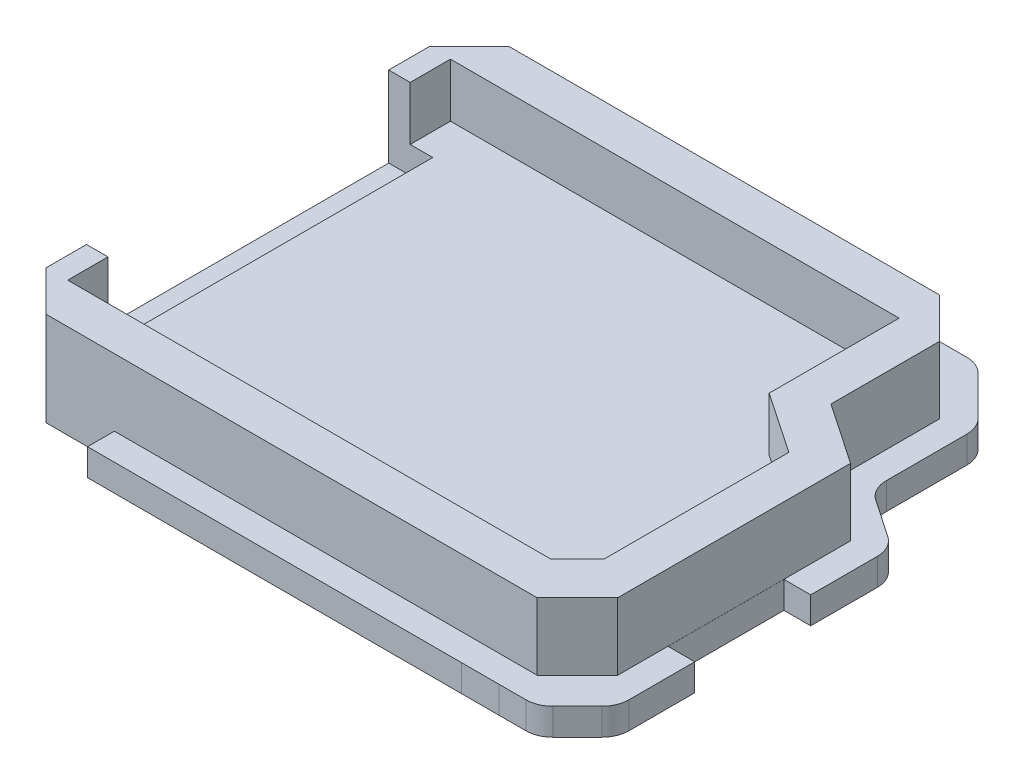
SolidWorks part; units mm, degrees
ref_plane "Front Plane" through (0, 0, 0) normal (0, 0, 1) x (1, 0, 0)
ref_plane "Top Plane" through (0, 0, 0) normal (0, 1, 0) x (1, 0, 0)
ref_plane "Right Plane" through (0, 0, 0) normal (1, 0, 0) x (0, 0, -1)
sketch "Sketch1" plane through (0, 0, 0) normal (0, 1, 0) x (1, 0, 0)
  line L0 (-34.6415, 17.5848) -> (-34.6415, -16.9152)
  line L1 (-31.6415, 14.5848) -> (3.3585, 14.5848)
  line L2 (-31.6415, 14.5848) -> (-31.6415, -13.9152)
  line L3 (-31.6415, -13.9152) -> (3.3585, -13.9152)
  line L4 (3.3585, 14.5848) -> (3.3585, -13.9152)
  line L5 (-34.6415, -16.9152) -> (6.3585, -16.9152)
  line L6 (6.3585, 17.5848) -> (6.3585, -16.9152)
  line L7 (-34.6415, 17.5848) -> (6.3585, 17.5848)
  dimension "D1" = 3
extrude "Boss-Extrude1" add sketch "Sketch1" along normal blind 5
sketch "Sketch2" plane through (0, 0, 0) normal (0, 1, 0) x (1, 0, 0)
  line L1 (-31.6415, 14.5848) -> (3.3585, 14.5848)
  line L2 (-31.6415, 14.5848) -> (-31.6415, -13.9152)
  line L3 (-31.6415, -13.9152) -> (3.3585, -13.9152)
  line L4 (3.3585, 14.5848) -> (3.3585, -13.9152)
extrude "Boss-Extrude2" add sketch "Sketch2" along normal blind 1
sketch "Sketch6" plane through (-34.6415, 0, 0) normal (-1, 0, 0) x (0, 0, 1)
  line L1 (-17.5848, 5) -> (16.9152, 5)
  line L2 (-17.5848, 5) -> (-17.5848, 0)
  line L3 (-17.5848, 0) -> (16.9152, 0)
  line L4 (16.9152, 5) -> (16.9152, 0)
extrude "Cut-Extrude2" cut sketch "Sketch6" against normal blind 3
sketch "Sketch7" plane through (0, 1, 0) normal (0, 1, 0) x (1, 0, 0)
  line L1 (-31.6415, 14.5848) -> (-30.0415, 14.5848)
  line L2 (-31.6415, 14.5848) -> (-31.6415, 11.5848)
  line L3 (-31.6415, 11.5848) -> (-30.0415, 11.5848)
  line L4 (-30.0415, 14.5848) -> (-30.0415, 11.5848)
  line L5 (-31.6415, -13.9152) -> (-30.0415, -13.9152)
  line L6 (-31.6415, -13.9152) -> (-31.6415, -10.9152)
  line L7 (-31.6415, -10.9152) -> (-30.0415, -10.9152)
  line L8 (-30.0415, -13.9152) -> (-30.0415, -10.9152)
extrude "Boss-Extrude3" add sketch "Sketch7" along normal blind 4
chamfer "Chamfer1" distance 3 angle 45 4 edges at (6.3585, 2.5, -17.5848) (6.3585, 2.5, 16.9152) (-31.6415, 2.5, -17.5848) (-31.6415, 2.5, 16.9152)
sketch "Sketch14" plane through (0, 1, 0) normal (0, 1, 0) x (1, 0, 0)
  line L0 (167.1391, 423.2739) -> (1080.46, 418.4917) construction
  line L1 (3.3585, -13.9152) -> (3.3585, 14.5848) construction
  line L2 (3.3585, 3.0917) -> (6.8611, 3.0917)
  line L3 (3.3585, 3.0917) -> (3.3585, -17.3608)
  line L4 (3.3585, -17.3608) -> (6.8611, -17.3608)
  line L5 (6.8611, 3.0917) -> (6.8611, -17.3608)
extrude "Cut-Extrude6" cut sketch "Sketch14" along normal blind 10
sketch "Sketch17" plane through (0, 1, 0) normal (0, 1, 0) x (1, 0, 0)
  line L0 (3.3585, 3.0917) -> (7.91, 0)
  line L2 (10.91, 3.4196) -> (10.91, -16.9152)
  line L4 (7.91, 0) -> (7.91, -13.9152)
  line L5 (3.3585, -13.9152) -> (7.91, -13.9152)
  line L6 (3.3585, -13.9152) -> (3.3585, -16.9152)
  line L7 (3.3585, -16.9152) -> (10.91, -16.9152)
  line L9 (10.91, 3.4196) -> (3.3585, 8.5491)
  line L10 (3.3585, 3.0917) -> (3.3585, 14.5848) construction
  line L11 (3.3585, 8.5491) -> (3.3585, 3.0917)
extrude "Boss-Extrude5" add sketch "Sketch17" along normal blind 4
sketch "Sketch19" plane through (0, 0, 0) normal (0, -1, 0) x (1, 0, 0)
  line L0 (3.3585, 16.9152) -> (10.91, 16.9152)
  line L1 (10.91, 16.9152) -> (10.91, -3.4196)
  line L2 (10.91, -3.4196) -> (6.3585, -6.5113)
  line L3 (6.3585, -6.5113) -> (6.3585, 13.9152)
  line L4 (6.3585, 13.9152) -> (3.3585, 16.9152)
extrude "Boss-Extrude7" add sketch "Sketch19" against normal blind 1
sketch "Sketch9" plane through (0, 1, 0) normal (0, 1, 0) x (1, 0, 0)
  line L1 (-31.6415, 11.5848) -> (-28.3587, 11.5848)
  line L2 (-31.6415, 11.5848) -> (-31.6415, -10.8359)
  line L3 (-31.6415, -10.8359) -> (-28.3587, -10.8359)
  line L4 (-28.3587, 11.5848) -> (-28.3587, -10.8359)
extrude "Cut-Extrude3" cut sketch "Sketch9" against normal blind 4
sketch "Sketch11" plane through (0, 0, 0) normal (0, -1, 0) x (1, 0, 0)
  line L0 (-26.6655, 18.9152) -> (-31.6415, 13.9152)
  line L1 (-31.6415, 13.9152) -> (-31.6415, -14.5848)
  line L2 (-31.6415, -14.5848) -> (-26.6292, -19.5848)
  line L3 (-26.6292, -19.5848) -> (4.2338, -19.5848)
  line L4 (4.2338, -19.5848) -> (8.3585, -15.4601)
  line L5 (8.3585, -15.4601) -> (8.3585, 14.7437)
  line L6 (8.3585, 14.7437) -> (4.264, 18.9152)
  line L7 (4.264, 18.9152) -> (-26.6655, 18.9152)
extrude "Boss-Extrude4" add sketch "Sketch11" along normal blind 2
sketch "Sketch12" plane through (0, 0, 0) normal (0, 1, 0) x (1, 0, 0)
  line L1 (-28.3587, 11.5848) -> (-31.6415, 11.5848)
  line L2 (-28.3587, 11.5848) -> (-28.3587, -10.8359)
  line L3 (-28.3587, -10.8359) -> (-31.6415, -10.8359)
  line L4 (-31.6415, 11.5848) -> (-31.6415, -10.8359)
extrude "Cut-Extrude4" cut sketch "Sketch12" against normal blind 1
sketch "Sketch20" plane through (0, 0, 0) normal (0, -1, 0) x (1, 0, 0)
  line L0 (6.227, 16.9152) -> (10.91, 16.9152)
  line L1 (10.91, 16.9152) -> (10.91, -3.4196)
  line L2 (10.91, -3.4196) -> (8.3585, -5.1528)
  line L3 (8.3585, -5.1528) -> (8.3585, 14.7437)
  line L4 (8.3585, 14.7437) -> (6.227, 16.9152)
extrude "Boss-Extrude8" add sketch "Sketch20" along normal blind 2
sketch "Sketch21" plane through (0, 0, 0) normal (0, 1, 0) x (1, 0, 0)
  line L0 (6.3585, 6.5113) -> (10.9077, 3.4212)
  line L1 (10.9077, 3.4212) -> (10.9077, -16.9128)
  line L2 (10.9077, -16.9128) -> (6.227, -16.9152)
  line L3 (6.227, -16.9152) -> (4.264, -18.9152)
  line L4 (7.4822, 8.1657) -> (12.9077, 4.4804)
  line L5 (12.9077, 4.4804) -> (12.9077, -18.9117)
  line L6 (12.9077, -18.9117) -> (7.0668, -18.9148)
  line L7 (7.0668, -18.9148) -> (5.6913, -20.3162)
  line L8 (7.0668, -18.9148) -> (4.264, -18.9152)
  line L9 (8.3585, 7.5705) -> (8.3585, 5.1528)
  line L10 (8.3585, 15.4601) -> (8.3585, 5.1528) construction
  line M10 (8.3585, 5.1528) -> (8.3585, 15.4601)
  dimension "D1" = 2
extrude "Boss-Extrude9" add sketch "Sketch21" against normal blind 2 contours L8 L6 L5 L4 L0 L1 L2 L3 M10
sketch "Sketch22" plane through (0, 1, 0) normal (0, 1, 0) x (1, 0, 0)
  line L0 (167.2956, 423.4871) -> (1080.6164, 418.7049) construction
sketch "Sketch23" plane through (0, 5, 0) normal (0, 1, 0) x (1, 0, 0)
  line L1 (9.2243, 0.938) -> (-3.3619, 9.4687)
  line L2 (9.2243, 0.938) -> (4.6728, 4.0297)
  line L3 (9.2243, 0.938) -> (4.6728, 4.0297)
  line L4 (-3.3619, 9.4687) -> (16.5933, -4.0566)
  line L5 (7.91, -4.2447) -> (7.91, 10.1169)
  line L6 (7.91, 0) -> (7.91, -13.9152) construction
  line L7 (3.3585, 4.9137) -> (3.3585, 3.0917)
  line L8 (3.3585, 3.0917) -> (7.91, 0)
  line L9 (7.91, 0) -> (7.91, 1.8288)
  line L10 (7.91, 1.8288) -> (3.3585, 4.9137)
  line M11 (3.3585, 14.5848) -> (3.3585, 3.0917)
  line M12 (3.3585, 3.0917) -> (7.91, 0)
  dimension "D1" = 3
extrude "Cut-Extrude7" cut sketch "Sketch23" against normal blind 4 and the other way through all contours L5 L4 M12 M11
chamfer "Chamfer2" distance 3 angle 45 2 edges at (12.9077, -1, 18.9117) (10.91, 2.5, 16.9152)
chamfer "Chamfer3" distance 2 angle 45 1 edges at (7.91, 3, 13.9152)
sketch "Sketch26" plane through (0, 0, 18.9152) normal (0, 0, 1) x (1, 0, 0)
  line L2 (-23.5655, -2) -> (-23.5655, 0)
  line L3 (-23.5655, -2) -> (-23.5655, 0)
  dimension "D1" = 3.1
sketch "Sketch27" plane through (0, 0, 0) normal (0, 1, 0) x (1, 0, 0)
  line L0 (-23.5646, -18.9152) -> (-23.5646, -16.9567)
  line L1 (4.264, -18.9152) -> (-26.6655, -18.9152) construction
  line L2 (-23.5646, -16.9567) -> (-23.5646, -16.9152)
  line L3 (-28.6415, -16.9152) -> (7.91, -16.9152) construction
  line L4 (-23.5646, -16.9152) -> (-28.6415, -16.9152)
  line L5 (-28.6415, -16.9152) -> (-26.6655, -18.9152)
  line L6 (-26.6655, -18.9152) -> (-23.5646, -18.9152)
extrude "Cut-Extrude8" cut sketch "Sketch27" against normal blind 10
sketch "Sketch29" plane through (-22.9503, 0, 22.6754) normal (0.7114, 0, -0.7028) x (-0.7028, 0, -0.7114)
  line L1 (8.0975, 0) -> (5.286, 0)
  line L2 (8.0975, 0) -> (8.0975, -2)
  line L3 (8.0975, -2) -> (5.286, -2)
  line L4 (5.286, 0) -> (5.286, -2)
extrude "Cut-Extrude9" cut sketch "Sketch29" against normal blind 10
sketch "Sketch30" plane through (0, 0, -19.5848) normal (0, 0, -1) x (-1, 0, 0)
  line L2 (23.5292, -2) -> (23.5292, 0)
  line L3 (23.5292, -2) -> (23.5292, 0)
  dimension "D1" = 3.1
sketch "Sketch31" plane through (0, 0, 0) normal (0, 1, 0) x (1, 0, 0)
  line L1 (-23.5347, 19.587) -> (-28.7947, 19.587)
  line L2 (-23.5347, 19.587) -> (-23.5347, 17.587)
  line L3 (-23.5347, 17.587) -> (-28.7947, 17.587)
  line L4 (-28.7947, 19.587) -> (-28.7947, 17.587)
extrude "Cut-Extrude10" cut sketch "Sketch31" against normal blind 10
sketch "Sketch33" plane through (0, -2, 0) normal (0, -1, 0) x (1, 0, 0)
  line L0 (12.9077, -4.4804) -> (12.9077, 15.9117) construction
  line L1 (12.9077, 10.1783) -> (10.9143, 10.1783)
  line L2 (12.9077, 10.1783) -> (12.9077, 1.5449)
  line L3 (12.9077, 1.5449) -> (10.9143, 1.5449)
  line L4 (10.9143, 10.1783) -> (10.9143, 1.5449)
extrude "Cut-Extrude11" cut sketch "Sketch33" against normal blind 10
fillet "Fillet1" radius 2 6 edges at (9.9061, -1, 18.9133) (12.9077, -1, 15.9117) (4.2338, -1, -19.5848) (8.3585, -1, -15.4601) (8.3585, -1, -7.5705) (12.9077, -1, -4.4804)
sketch "Sketch34" plane through (0, -2, 0) normal (0, -1, 0) x (1, 0, 0)
  line L0 (-380.8983, 125.0738) -> (-380.8983, 664.4071) construction
  arc A0 (-25.0847, 4.3342) -> (-24.1395, 3.856) centre (-24.7331, 3.856) ccw
  arc A1 (-18.9614, 4.9413) -> (-19.4854, 5.808) centre (-19.3017, 5.3273) ccw
  arc A2 (-18.2262, 4.0153) -> (-18.5543, 4.5578) centre (-18.2741, 4.3568) ccw
  arc A3 (-18.3563, -6.3906) -> (-18.8066, -6.8108) centre (-18.5894, -6.5922) ccw
  arc A4 (-6.8242, -9.8947) -> (-7.3662, -9.297) centre (-7.1006, -9.6007) ccw
  arc A5 (-14.1967, -3.6031) -> (-14.4962, -4.791) centre (-14.1967, -4.2348) ccw
  spline S0 degree 2 poles (-24.0908, -14.6074) (-21.8602, -7.3014) (-22.8581, 0.2234) knots 0 0 0 1 1 1
  spline S1 degree 2 poles (-24.3523, 1.2694) (-27.5714, -2.2007) (-28.7605, -6.7998) knots 0 0 0 1 1 1
  spline S2 degree 2 poles (-30.2921, -14.6074) (-30.9427, -11.4487) (-29.7318, -8.5182) knots 0 0 0 1 1 1
  spline S3 degree 2 poles (-28.7605, -6.7998) (-28.6557, -8.0311) (-29.7318, -8.5182) knots 0 0 0 1 1 1
  spline S4 degree 2 poles (-22.8581, 0.2234) (-22.9627, 2.1229) (-24.7331, 2.3127) knots 0 0 0 1 1 1
  spline S5 degree 1 poles (-24.7331, 2.3127) (-24.3523, 1.2694) knots 0 0 1 1
  spline S6 degree 2 poles (-24.1395, 3.856) (-23.5269, 5.4838) (-21.8044, 5.3273) knots 0 0 0 1 1 1
  spline S7 degree 2 poles (-21.8044, 5.3273) (-21.4255, 5.1371) (-21.407, 4.725) knots 0 0 0 1 1 1
  spline S8 degree 2 poles (-21.407, 4.725) (-21.4304, 2.8975) (-19.8914, 1.9439) knots 0 0 0 1 1 1
  spline S9 degree 2 poles (-19.8914, 1.9439) (-18.9568, 1.5722) (-18.2741, 2.3127) knots 0 0 0 1 1 1
  spline S10 degree 2 poles (-18.2741, 2.3127) (-16.8059, 3.9488) (-17.6253, 6.3584) knots 0 0 0 1 1 1
  spline S11 degree 2 poles (-17.6253, 6.3584) (-19.6974, 7.0565) (-21.201, 5.446) knots 0 0 0 1 1 1
  spline S12 degree 2 poles (-21.201, 5.446) (-21.1025, 6.7088) (-19.8914, 6.844) knots 0 0 0 1 1 1
  spline S13 degree 2 poles (-19.8914, 6.844) (-18.7343, 7.0004) (-17.6253, 6.6233) knots 0 0 0 1 1 1
  spline S14 degree 2 poles (-17.6253, 6.6233) (-15.5977, 4.4416) (-17.743, 2.091) knots 0 0 0 1 1 1
  spline S15 degree 2 poles (-17.743, 2.091) (-17.6876, 1.2845) (-16.8454, 1.9439) knots 0 0 0 1 1 1
  spline S16 degree 2 poles (-10.4149, 6.8734) (-10.952, 5.8396) (-12.1071, 5.446) knots 0 0 0 1 1 1
  spline S17 degree 2 poles (-12.1071, 5.446) (-14.9143, 4.3222) (-16.8454, 1.9439) knots 0 0 0 1 1 1
  spline S18 degree 3 poles (-25.0847, 4.3342) (-23.1823, 7.9151) (-20.0149, 9.8924) (-15.5826, 10.2661) knots 0.041835 0.041835 0.041835 0.041835 1 1 1 1
  spline S19 degree 2 poles (-10.4149, 6.8734) (-11.7795, 8.9293) (-14.1967, 9.5696) knots 0 0 0 1 1 1
  spline S20 degree 2 poles (-15.5826, 10.2661) (-15.2749, 8.9563) (-14.1967, 9.5696) knots 0 0 0 1 1 1
  spline S21 degree 1 poles (-30.2921, -14.6074) (-24.0908, -14.6074) knots 0 0 1 1
  spline S22 degree 2 poles (-21.0097, -2.0604) (-21.7372, -8.3632) (-22.8581, -14.6074) knots 0 0 0 1 1 1
  spline S23 degree 1 poles (-22.8581, -14.6074) (-7.3406, -14.2392) knots 0 0 1 1
  spline S24 degree 2 poles (-7.3406, -14.2392) (-8.9178, -12.0287) (-11.4814, -11.2724) knots 0 0 0 1 1 1
  spline S25 degree 2 poles (-11.4814, -11.2724) (-15.758, -9.9977) (-18.8172, -6.7998) knots 0 0 0 1 1 1
  spline S26 degree 2 poles (-18.3563, -6.3906) (-16.1505, -8.6372) (-13.3783, -10.1239) knots 0 0 0 1 1 1
  spline S27 degree 2 poles (-13.3783, -10.1239) (-10.5507, -11.4655) (-7.5708, -10.5549) knots 0 0 0 1 1 1
  spline S28 degree 3 poles (-6.7345, -9.7704) (-6.8591, -9.9445) (-7.0864, -10.2624) (-7.42, -10.4638) (-7.5708, -10.5549) knots 0 0 0 0 0.548043 1 1 1 1
  spline S29 degree 2 poles (-21.0097, -2.0604) (-18.7817, -2.3871) (-17.6253, -4.3119) knots 0 0 0 1 1 1
  spline S30 degree 2 poles (-17.6253, -4.3119) (-17.2455, -4.8549) (-16.5717, -4.7052) knots 0 0 0 1 1 1
  spline S31 degree 2 poles (-16.5717, -4.7052) (-15.272, -4.8545) (-14.6183, -6.2021) knots 0 0 0 1 1 1
  spline S32 degree 1 poles (-14.6183, -6.2021) (-14.734, -6.2828) knots 0 0 1 1
  spline S33 degree 1 poles (-14.734, -6.2828) (-15.9137, -5.5707) knots 0 0 1 1
  spline S34 degree 2 poles (-15.9137, -5.5707) (-12.9705, -9.0275) (-8.5896, -10.1704) knots 0 0 0 1 1 1
  spline S35 degree 1 poles (-8.5896, -10.1704) (-7.3662, -9.297) knots 0 0 1 1
  spline S36 degree 2 poles (-4.6801, -7.4619) (-2.5162, -10.5714) (-2.6564, -14.4122) knots 0 0 0 1 1 1
  spline S37 degree 1 poles (-2.6564, -14.4122) (-6.905, -14.1474) knots 0 0 1 1
  spline S38 degree 2 poles (-6.0786, -8.2459) (-6.0663, -9.9177) (-7.3662, -10.909) knots 0 0 0 1 1 1
  spline S39 degree 2 poles (-7.3662, -10.909) (-7.963, -12.5531) (-6.905, -14.1474) knots 0 0 0 1 1 1
  spline S40 degree 2 poles (-6.0786, -8.2459) (-5.4843, -7.665) (-4.6801, -7.4619) knots 0 0 0 1 1 1
  spline S41 degree 1 poles (-7.2458, -1.1934) (-9.1512, -3.0256) knots 0 0 1 1
  spline S42 degree 2 poles (-4.8761, -7.0075) (-9.7012, -6.7464) (-14.1967, -5.0288) knots 0 0 0 1 1 1
  spline S43 degree 1 poles (-14.1967, -5.0288) (-14.6704, -4.6528) knots 0 0 1 1
  spline S44 degree 2 poles (-14.1967, -3.6031) (-12.0094, -3.3225) (-9.8475, -3.7951) knots 0 0 0 1 1 1
  spline S45 degree 1 poles (-9.1512, -3.0256) (-7.3662, -4.2348) knots 0 0 1 1
  spline S46 degree 2 poles (-7.3662, -4.2348) (-8.8524, -4.9683) (-9.8475, -3.7951) knots 0 0 0 1 1 1
  spline S47 degree 2 poles (-7.2458, -1.1934) (-7.1162, -3.8801) (-4.8761, -5.4074) knots 0 0 0 1 1 1
  spline S48 degree 1 poles (-4.8761, -7.0075) (-6.0786, -5.7861) knots 0 0 1 1
  spline S49 degree 2 poles (-4.8761, -5.4074) (-5.0533, -5.787) (-5.4111, -5.3841) knots 0 0 0 1 1 1
  spline S50 degree 2 poles (-5.4111, -5.3841) (-7.6104, -3.6757) (-6.0363, -5.829) knots 0 0 0 1 1 1
  spline S51 degree 2 poles (-19.3017, 5.8419) (-21.1362, 5.5584) (-20.45, 3.6137) knots 0 0 0 1 1 1
  spline S52 degree 2 poles (-20.45, 3.6137) (-19.6703, 2.4497) (-18.3563, 2.895) knots 0 0 0 1 1 1
  spline S53 degree 2 poles (-18.2262, 4.0153) (-18.9915, 3.8237) (-19.7835, 3.856) knots 0 0 0 1 1 1
  spline S54 degree 2 poles (-19.7835, 3.856) (-19.1168, 3.3052) (-18.3563, 2.895) knots 0 0 0 1 1 1
  spline S55 degree 2 poles (-18.9614, 4.9413) (-19.2087, 4.2882) (-18.5543, 4.5578) knots 0 0 0 1 1 1
  spline S56 degree 3 poles (-17.388, 1.2694) (-14.0408, 3.3664) (-11.0604, 6.169) (-6.635, 6.0928) knots 0 0 0 0 1 1 1 1
  spline S57 degree 2 poles (-6.635, 6.0928) (-4.1943, 5.7741) (-4.6801, 2.895) knots 0 0 0 1 1 1
  spline S58 degree 2 poles (-4.6801, 2.895) (-4.8989, 1.8554) (-5.7316, 3.0622) knots 0 0 0 1 1 1
  spline S59 degree 2 poles (-5.7316, 3.0622) (-8.5372, 3.981) (-11.1224, 2.1658) knots 0 0 0 1 1 1
  spline S60 degree 2 poles (-11.1224, 2.1658) (-12.9905, 0.9841) (-14.6704, -0.4407) knots 0 0 0 1 1 1
  spline S61 degree 2 poles (-14.6704, -0.4407) (-17.0583, -2.4318) (-20.0565, -1.7724) knots 0 0 0 1 1 1
  spline S62 degree 2 poles (-20.0565, -1.7724) (-21.8174, -0.7481) (-21.8044, 1.2694) knots 0 0 0 1 1 1
  spline S63 degree 2 poles (-21.8044, 1.2694) (-21.404, 2.1619) (-20.6244, 1.3885) knots 0 0 0 1 1 1
  spline S64 degree 2 poles (-20.6244, 1.3885) (-19.7185, 0.5455) (-18.733, 1.3737) knots 0 0 0 1 1 1
  spline S65 degree 2 poles (-18.733, 1.3737) (-18.0339, 1.7326) (-17.388, 1.2694) knots 0 0 0 1 1 1
